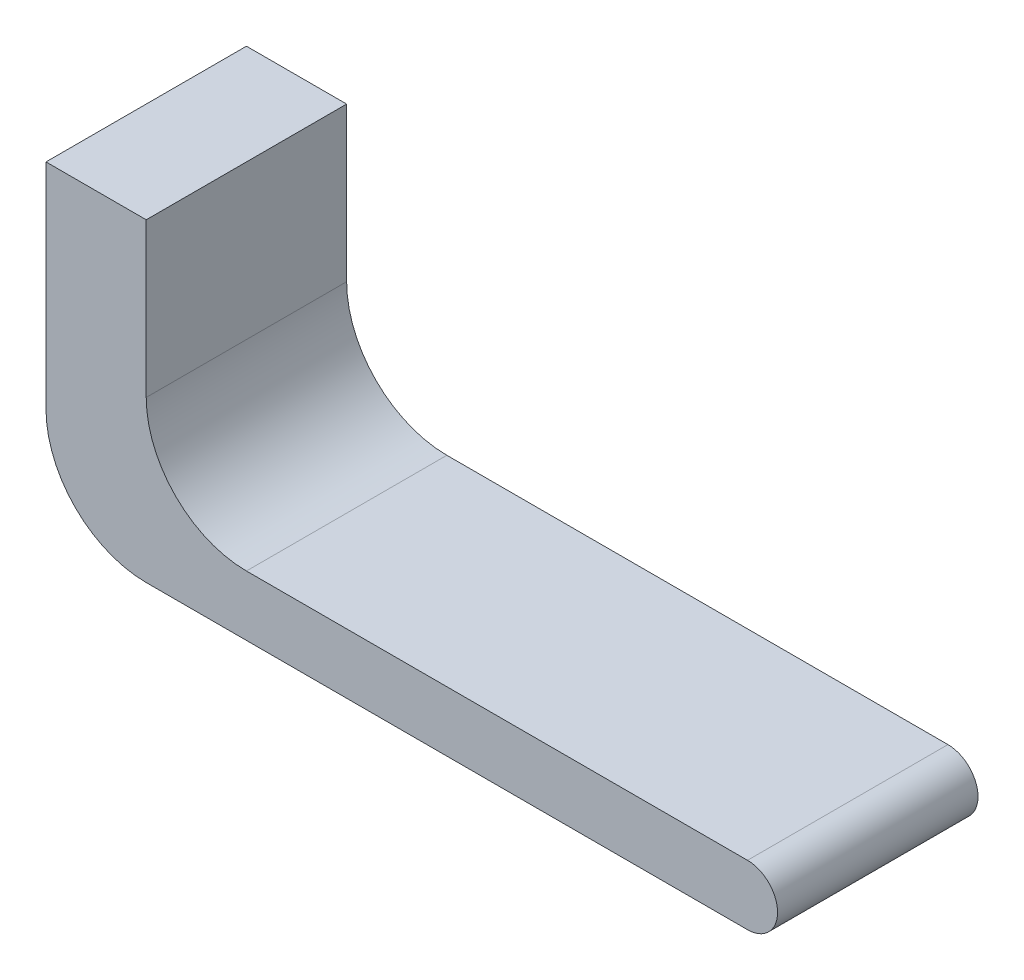
SolidWorks part; units mm, degrees
material "PLA-填充率10%"
ref_plane "前视基准面" through (0, 0, 0) normal (0, 0, 1) x (1, 0, 0)
ref_plane "上视基准面" through (0, 0, 0) normal (0, 1, 0) x (1, 0, 0)
ref_plane "右视基准面" through (0, 0, 0) normal (1, 0, 0) x (0, 0, -1)
sketch "草图1" plane through (0, 0, 0) normal (0, 0, 1) x (1, 0, 0)
  line L0 (0, 0) -> (-30, 0) construction
  line L1 (0, -1.5) -> (-30, -1.5)
  line L2 (0, 1.5) -> (-25, 1.5)
  line L4 (-30, -1.5) -> (-35, -1.5)
  line L5 (-30, 6.5) -> (-30, 14.1761)
  line L6 (-30, 14.1761) -> (-35, 14.1761)
  line L7 (-35, -1.5) -> (-35, 14.1761)
  arc A0 (0, -1.5) -> (0, 1.5) centre (0, 0) ccw
  arc A2 (-25, 1.5) -> (-30, 6.5) centre (-25, 6.5) cw
  point P3 (-15, 0)
  point P12 (0, 0)
  point P13 (-30, 0)
  dimension "D1" = 1.5
  dimension "D3" = 5
  dimension "D2" = 30
  dimension "D4" = 5
extrude "凸台-拉伸1" add sketch "草图1" along normal blind 10
fillet "圆角1" radius 5 1 edges at (-35, -1.5, 5)
